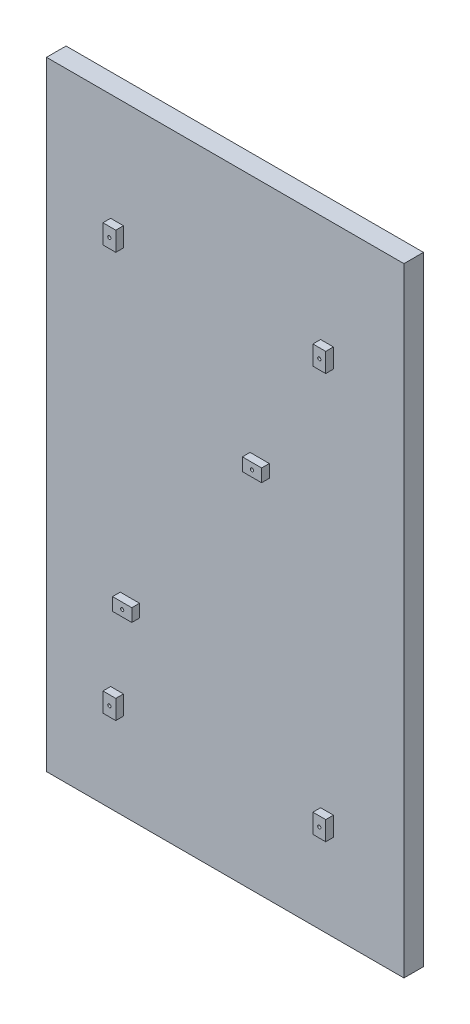
SolidWorks part; units mm, degrees
ref_plane "Front Plane" through (0, 0, 0) normal (0, 0, 1) x (1, 0, 0)
ref_plane "Top Plane" through (0, 0, 0) normal (0, 1, 0) x (1, 0, 0)
ref_plane "Right Plane" through (0, 0, 0) normal (1, 0, 0) x (0, 0, -1)
sketch "Sketch1" plane through (0, 0, 0) normal (0, 0, 1) x (1, 0, 0)
  line L0 (0, 0) -> (0, 193)
  line L1 (0, 193) -> (111.5, 193)
  line L2 (111.5, 193) -> (111.5, 0)
  line L3 (111.5, 0) -> (0, 0)
extrude "Boss-Extrude1" add sketch "Sketch1" along normal blind 6.1
sketch "Sketch2" plane through (0, 0, 6.1) normal (0, 0, 1) x (1, 0, 0)
  line L1 (20, 159.5) -> (24, 159.5)
  line L7 (87.5, 33) -> (85.5, 33)
  line L8 (85.5, 33) -> (85.5, 27)
  line L9 (85.5, 27) -> (89.5, 27)
  line L10 (89.5, 27) -> (89.5, 33)
  line L11 (89.5, 33) -> (87.5, 33)
  line L12 (20, 33) -> (24, 33)
  line L13 (20, 33) -> (20, 27)
  line L14 (20, 27) -> (24, 27)
  line L15 (24, 33) -> (24, 27)
  line L16 (20, 159.5) -> (20, 153.5)
  line L17 (20, 153.5) -> (24, 153.5)
  line L18 (24, 159.5) -> (24, 153.5)
  line L19 (85.5, 159.5) -> (89.5, 159.5)
  line L20 (85.5, 159.5) -> (85.5, 153.5)
  line L21 (85.5, 153.5) -> (89.5, 153.5)
  line L22 (89.5, 159.5) -> (89.5, 153.5)
  line L23 (23, 60) -> (29, 60)
  line L24 (23, 60) -> (23, 56)
  line L25 (23, 56) -> (29, 56)
  line L26 (29, 60) -> (29, 56)
  line L27 (63.5, 118) -> (69.5, 118)
  line L28 (63.5, 118) -> (63.5, 114)
  line L29 (63.5, 114) -> (69.5, 114)
  line L30 (69.5, 118) -> (69.5, 114)
  circle A0 centre (22, 30) radius 0.5
  circle A1 centre (26, 58) radius 0.5
  circle A2 centre (87.5, 30) radius 0.5
  circle A3 centre (66.5, 116) radius 0.5
  circle A4 centre (22, 156.5) radius 0.5
  circle A5 centre (87.5, 156.5) radius 0.5
  point P0 (22, 30)
  point P1 (87.5, 30)
  point P2 (87.5, 156.5)
  point P3 (22, 156.5)
  point P4 (24, 153.5)
  point P5 (24, 27)
  point P6 (20, 159.5)
  point P8 (20, 33)
  point P21 (85.5, 159.5)
  point P24 (89.5, 153.5)
  point P27 (29, 56)
  point P28 (66.5, 58)
  point P29 (26, 116)
  point P30 (66.5, 116)
  point P31 (23, 60)
  point P32 (66.5, 116)
  point P33 (63.5, 118)
  point P34 (26, 58)
  point P36 (69.5, 114)
extrude "Boss-Extrude2" add sketch "Sketch2" along normal blind 2.4
